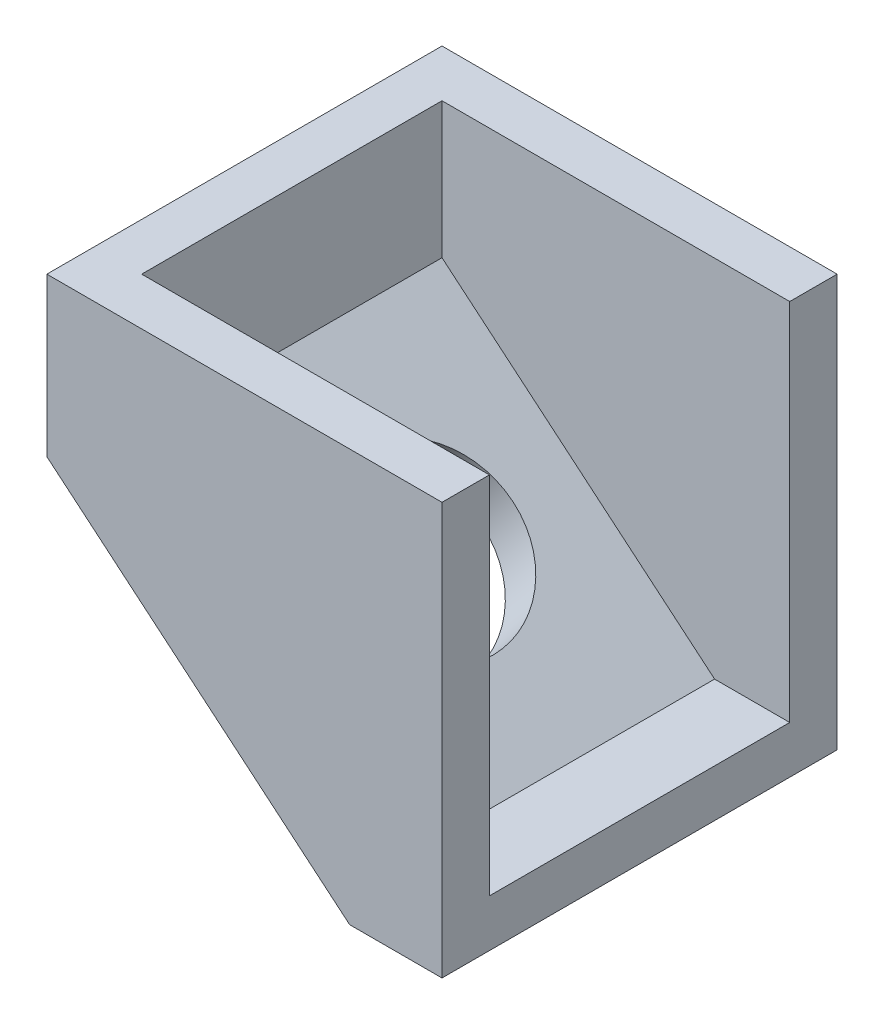
SolidWorks part; units mm, degrees
ref_plane "Front Plane" through (0, 0, 0) normal (0, 0, 1) x (1, 0, 0)
ref_plane "Top Plane" through (0, 0, 0) normal (0, 1, 0) x (1, 0, 0)
ref_plane "Right Plane" through (0, 0, 0) normal (1, 0, 0) x (0, 0, -1)
sketch "Sketch1" plane through (0, 0, 0) normal (0, 1, 0) x (1, 0, 0)
  line L1 (0, 0) -> (50, 0)
  line L2 (0, 0) -> (0, 50)
  line L3 (0, 50) -> (50, 50)
  line L4 (50, 0) -> (50, 50)
  dimension "D1" = 50
  dimension "D2" = 50
extrude "Boss-Extrude1" add sketch "Sketch1" along normal blind 52.13
sketch "Sketch2" plane through (0, 0, 0) normal (0, 0, 1) x (1, 0, 0)
  line L0 (0, 32.13) -> (0, 0)
  line L1 (0, 52.13) -> (0, 0) construction
  line L2 (0, 0) -> (38.3101, 0)
  line L3 (0, 0) -> (50, 0) construction
  line L4 (38.3101, 0) -> (0, 32.13)
  dimension "D1" = 20
  dimension "D2" = 50
  dimension "D3" = 50.014
extrude "Cut-Extrude1" cut sketch "Sketch2" against normal blind 52.13 contours L4 L0 L2
sketch "Sketch3" plane through (0, 52.13, 0) normal (0, 1, 0) x (1, 0, 0)
  line L0 (50, 50) -> (0, 50) construction
  line L1 (0, 44) -> (50, 44)
  line L2 (0, 44) -> (0, 6)
  line L3 (0, 6) -> (50, 6)
  line L4 (50, 44) -> (50, 6)
  line L6 (0, 0) -> (50, 0) construction
  line L7 (50, 0) -> (50, 50) construction
  line L8 (0, 50) -> (0, 0) construction
  point P6 (46.1459, 8.9927)
  point P8 (45.9879, -0.038)
  dimension "D1" = 6
  dimension "D2" = 6
  dimension "D3" = 0
  dimension "D4" = 0
extrude "Cut-Extrude2" cut sketch "Sketch3" against normal blind 52.13
sketch "Sketch4" plane through (0, 0, -44) normal (0, 0, 1) x (1, 0, 0)
  line L0 (0, 32.13) -> (38.3101, 0)
  line L1 (38.3101, 0) -> (42.1657, 4.5972)
  line L2 (42.1657, 4.5972) -> (3.8556, 36.7272)
  line L3 (3.8556, 36.7272) -> (0, 32.13)
  line L4 (50, 52.13) -> (50, 0) construction
  line L5 (38.3101, 0) -> (50, 0)
  line L6 (38.3101, 0) -> (38.3101, 6)
  line L7 (38.3101, 6) -> (50, 6)
  line L8 (50, 0) -> (50, 6)
  line L9 (0, 52.13) -> (50, 52.13) construction
  line L10 (6, 52.13) -> (0, 52.13)
  line L11 (6, 52.13) -> (6, 32.13)
  line L12 (6, 32.13) -> (0, 32.13)
  line L13 (0, 52.13) -> (0, 32.13)
  line M4 (38.3101, 0) -> (50, 0)
  line M5 (50, 0) -> (50, 52.13)
  line M6 (50, 52.13) -> (0, 52.13)
  line M7 (0, 52.13) -> (0, 32.13)
  line M8 (0, 32.13) -> (38.3101, 0)
  dimension "D1" = 6
  dimension "D2" = 6
  dimension "D3" = 6
extrude "Boss-Extrude3" add sketch "Sketch4" along normal up to surface (38 mm away) contours L7 L2 L1 M4 M5 | L7 L6 L1 L2 | L11 L12 L6 L7 L2 M8 | L11 L3 L2 M6 M7 up to face at (27.662, 27.278, -6)
sketch "Sketch5" plane through (15.8196, 18.8624, 0) normal (-0.6426, -0.7662, 0) x (0.7662, -0.6426, 0)
  line L1 (-20.6467, 0) -> (29.3533, 0)
  line L2 (-20.6467, 0) -> (-20.6467, -50)
  line L3 (-20.6467, -50) -> (29.3533, -50)
  line L4 (29.3533, 0) -> (29.3533, -50)
  circle A0 centre (4.3533, -25) radius 11
  dimension "D1" = 22
  dimension "D2" = 25
  dimension "D3" = 25
extrude "Cut-Extrude3" cut sketch "Sketch5" against normal blind 52.13 contours A0
